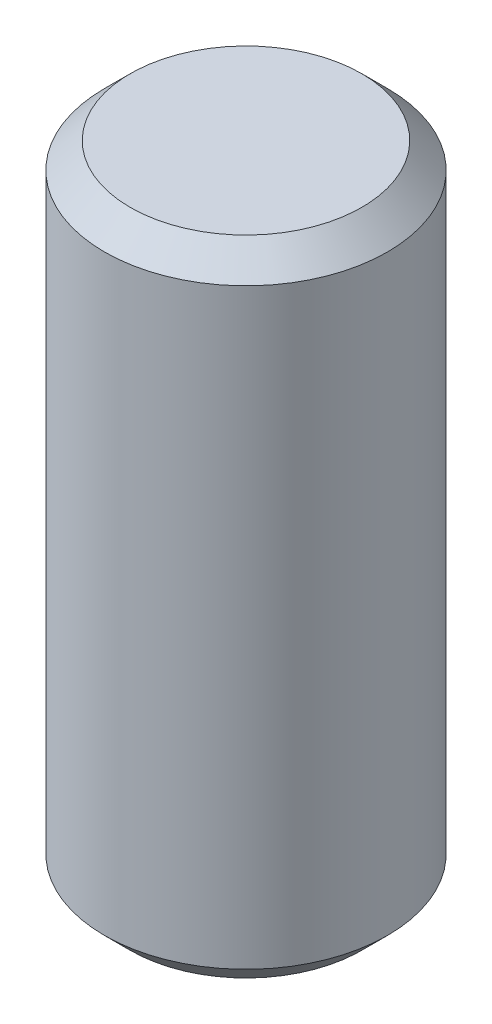
SolidWorks part; units mm, degrees
ref_plane "Front" through (0, 0, 0) normal (0, 0, 1) x (1, 0, 0)
ref_plane "Top" through (0, 0, 0) normal (0, 1, 0) x (1, 0, 0)
ref_plane "Right" through (0, 0, 0) normal (1, 0, 0) x (0, 0, -1)
sketch "Sketch1" plane through (0, 0, 0) normal (0, 0, 1) x (1, 0, 0)
  line L0 (0, 6.0802) -> (0, -6.0802) construction
  line L1 (0, -6.35) -> (2.794, -6.35)
  line L2 (2.794, -6.35) -> (2.794, 6.35)
  line L3 (2.794, 6.35) -> (0, 6.35)
  line L4 (0, 6.35) -> (0, -6.35)
  point P6 (0, 0)
  dimension "D1" = 5.588
  dimension "D2" = 12.7
revolve "Revolve1" add sketch "Sketch1" angle 360 about L0
chamfer "Chamfer1" distance 0.508 angle 45 2 edges at (0, -6.35, 2.794) (0, 6.35, 2.794)
